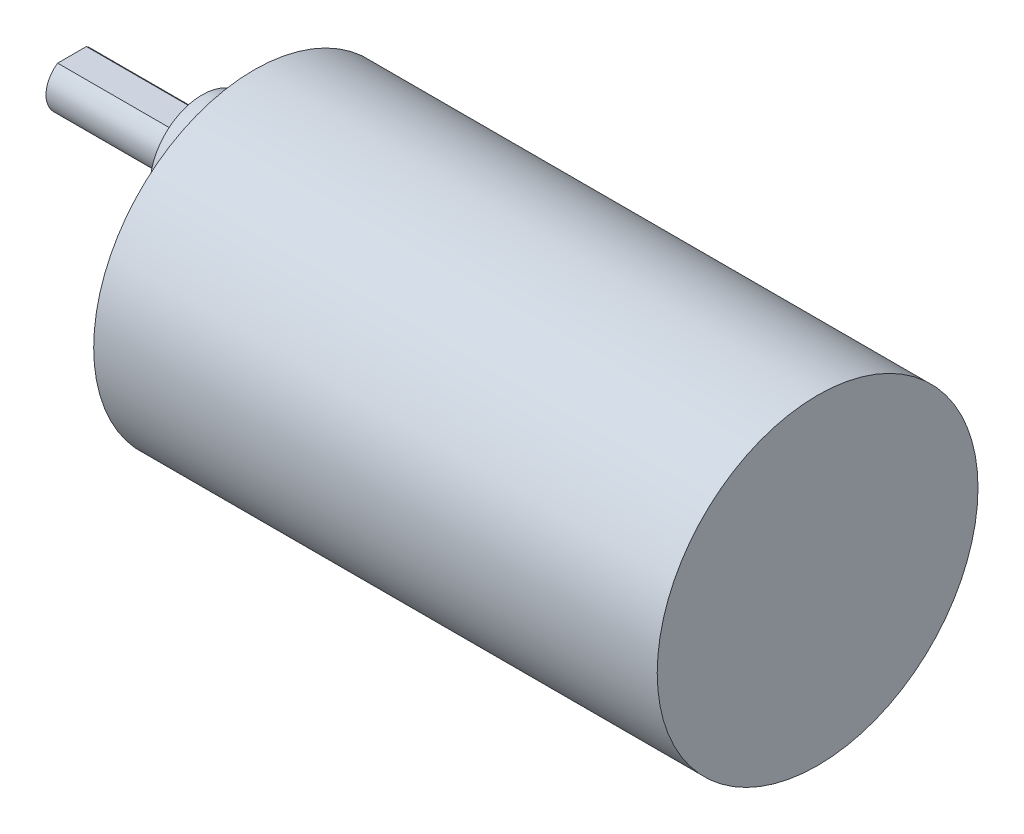
SolidWorks part; units mm, degrees
ref_plane "Ebene vorne" through (0, 0, 0) normal (0, 0, 1) x (1, 0, 0)
ref_plane "Ebene oben" through (0, 0, 0) normal (0, 1, 0) x (1, 0, 0)
ref_plane "Ebene rechts" through (0, 0, 0) normal (1, 0, 0) x (0, 0, -1)
sketch "Skizze1" plane through (0, 0, 0) normal (1, 0, 0) x (0, 0, -1)
  circle A0 centre (0, 0) radius 18.5
  dimension "D1" = 37
extrude "Aufsatz-Linear austragen1" add sketch "Skizze1" along normal blind 65 contours A0
sketch "Skizze2" plane through (0, 0, 0) normal (-1, 0, 0) x (0, 0, 1)
  circle A0 centre (0, 7) radius 6
  circle A1 centre (0, 7) radius 18.75 construction
  dimension "D1" = 12
  dimension "D2" = 37.5
  dimension "D3" = 7
extrude "Aufsatz-Linear austragen2" add sketch "Skizze2" along normal blind 6
sketch "Skizze3" plane through (-6, 0, 0) normal (-1, 0, 0) x (0, 0, 1)
  line L0 (-1.6583, 9.5) -> (1.6583, 9.5)
  circle A0 centre (0, 7) radius 3 construction
  arc A1 (-1.6583, 9.5) -> (1.6583, 9.5) centre (0, 7) ccw
  dimension "D1" = 6
  dimension "D2" = 2.5
  dimension "D3" = 7
extrude "Aufsatz-Linear austragen3" add sketch "Skizze3" along normal blind 15
